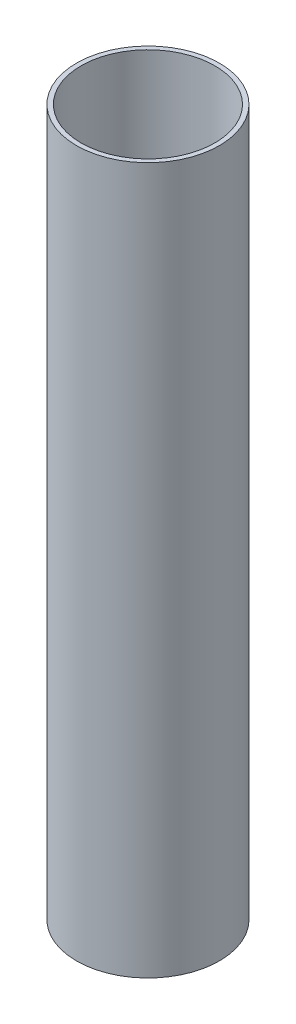
SolidWorks part; units mm, degrees
material "Alumina"
ref_plane "Front Plane" through (0, 0, 0) normal (0, 0, 1) x (1, 0, 0)
ref_plane "Top Plane" through (0, 0, 0) normal (0, 1, 0) x (1, 0, 0)
ref_plane "Right Plane" through (0, 0, 0) normal (1, 0, 0) x (0, 0, -1)
sketch "Sketch1" plane through (0, 0, 0) normal (0, 1, 0) x (1, 0, 0)
  circle A0 centre (0, 0) radius 25
  circle A1 centre (0, 0) radius 23.4
  dimension "D1" = 50
  dimension "D2" = 1.6
extrude "Boss-Extrude1" add sketch "Sketch1" along normal blind 247
